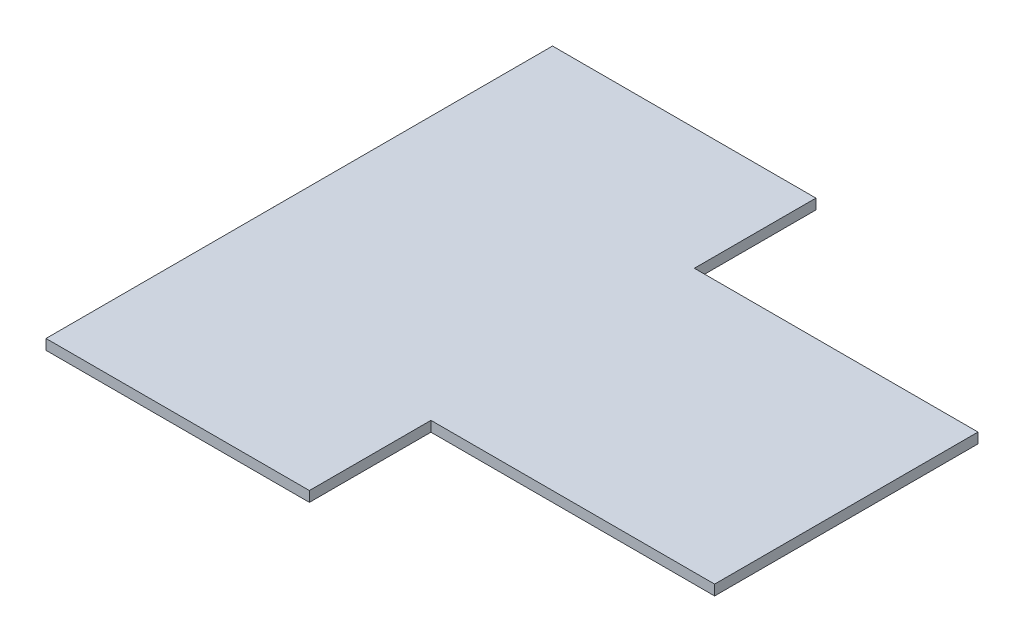
SolidWorks part; units mm, degrees
ref_plane "Front Plane" through (0, 0, 0) normal (0, 0, 1) x (1, 0, 0)
ref_plane "Top Plane" through (0, 0, 0) normal (0, 1, 0) x (1, 0, 0)
ref_plane "Right Plane" through (0, 0, 0) normal (1, 0, 0) x (0, 0, -1)
sketch "Sketch1" plane through (0, 0, 0) normal (0, 1, 0) x (1, 0, 0)
  line L0 (67.5, 32.5) -> (-2.5, 32.5)
  line L1 (-67.5, -62.5) -> (67.5, -62.5)
  line L2 (-67.5, -62.5) -> (-67.5, 62.5)
  line L3 (-67.5, 62.5) -> (67.5, 62.5)
  line L4 (67.5, -62.5) -> (67.5, 62.5)
  line L5 (-67.5, -62.5) -> (67.5, 62.5) construction
  line L6 (-67.5, 62.5) -> (67.5, -62.5) construction
  line L7 (-2.5, 32.5) -> (-2.5, 62.5)
  line L8 (67.5, -32.5) -> (-2.5, -32.5)
  line L9 (-2.5, -32.5) -> (-2.5, -62.5)
  point P0 (0, 0)
  dimension "D1" = 125
  dimension "D2" = 65
  dimension "D3" = 135
  dimension "D4" = 70
extrude "Boss-Extrude1" add sketch "Sketch1" along normal mid plane 2.54 contours L9 L8 L4 L0 L7 L3 L2 L1
